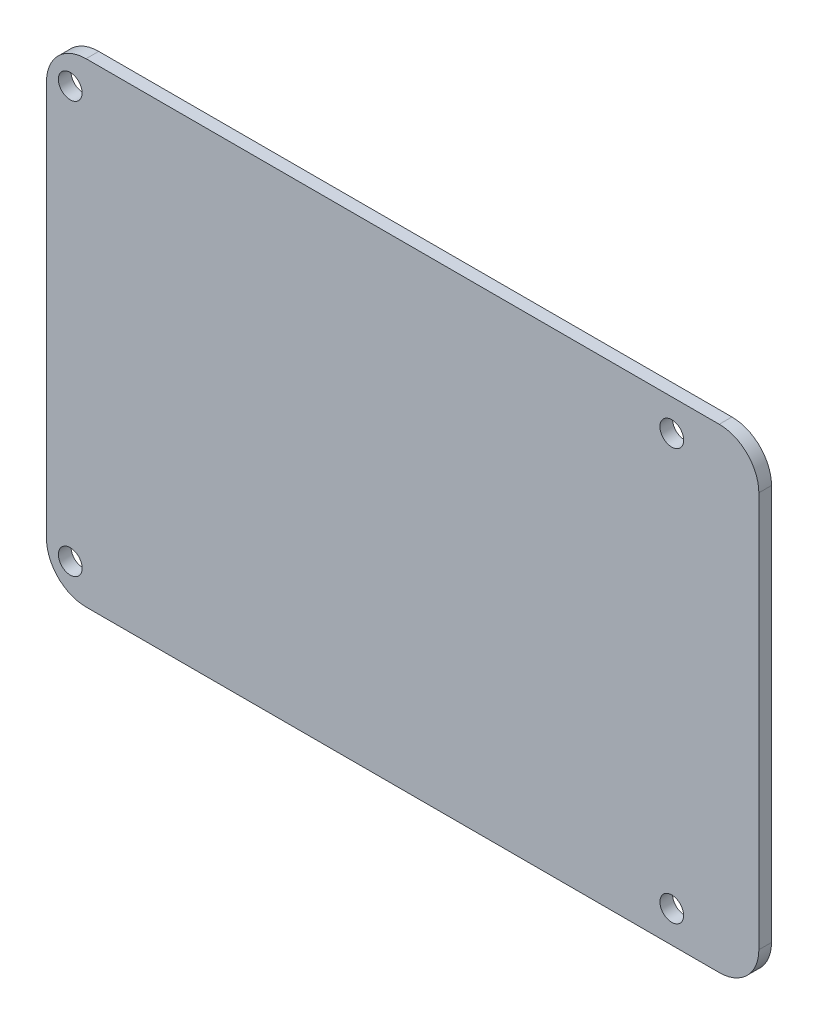
SolidWorks part; units mm, degrees
ref_plane "Front Plane" through (0, 0, 0) normal (0, 0, 1) x (1, 0, 0)
ref_plane "Top Plane" through (0, 0, 0) normal (0, 1, 0) x (1, 0, 0)
ref_plane "Right Plane" through (0, 0, 0) normal (1, 0, 0) x (0, 0, -1)
sketch "Sketch1" plane through (0, 0, 0) normal (0, 0, 1) x (1, 0, 0)
  line L1 (0, 0) -> (90, 0)
  line L2 (0, 0) -> (0, 60)
  line L3 (0, 60) -> (90, 60)
  line L4 (90, 0) -> (90, 60)
  dimension "D1" = 60
  dimension "D2" = 90
extrude "Boss-Extrude1" add sketch "Sketch1" along normal blind 1.6
fillet "Fillet1" radius 5 4 edges at (90, 0, 0.8) (90, 60, 0.8) (0, 0, 0.8) (0, 60, 0.8)
sketch "Sketch2" plane through (0, 0, 1.6) normal (0, 0, 1) x (1, 0, 0)
  line L0 (85, 60) -> (5, 60) construction
  line L1 (90, 5) -> (90, 55) construction
  line L2 (0, 55) -> (0, 5) construction
  circle A0 centre (79, 56) radius 1.5
  circle A1 centre (3, 56) radius 1.5
  dimension "D1" = 3
  dimension "D4" = 3
  dimension "D2" = 4
  dimension "D3" = 11
  dimension "D5" = 3
  dimension "D6" = 4
ref_plane "Plane1" through (0, 30, 0) normal (0, -1, 0) x (-1, 0, 0)
extrude "Cut-Extrude1" cut sketch "Sketch2" against normal up to next (1.6 mm away) contours A0 | A1
mirror "Mirror1" about plane through (0, 30, 0) normal (0, -1, 0) of "Cut-Extrude1"
